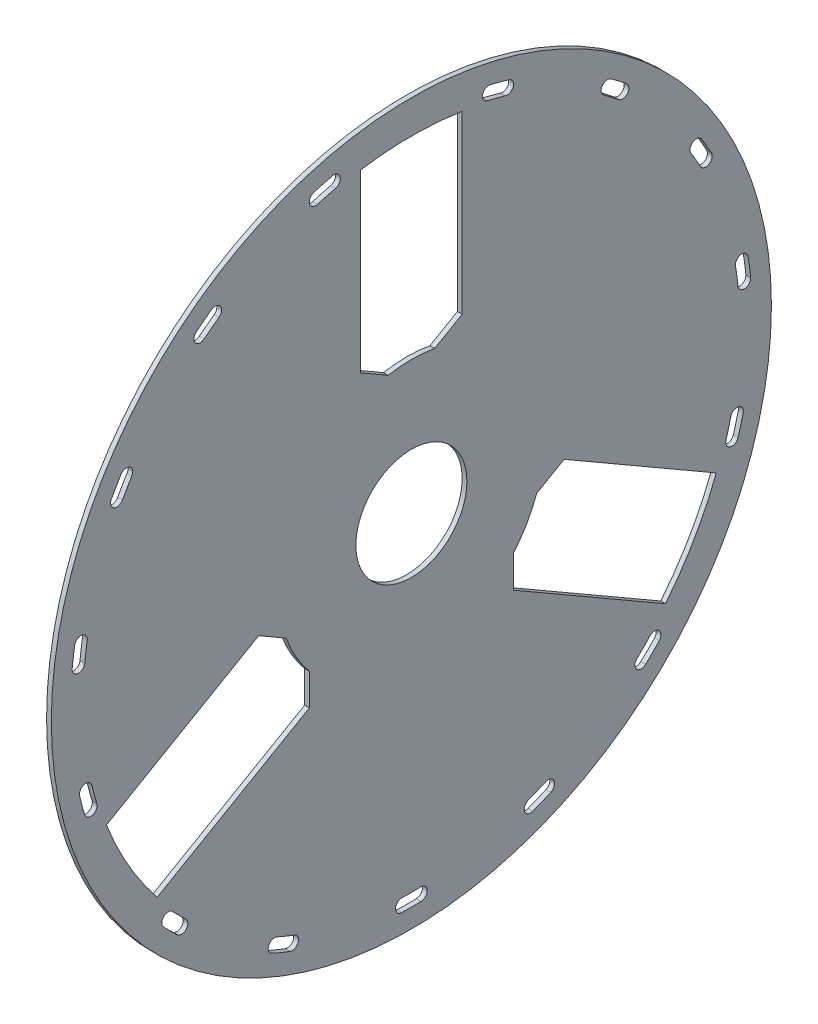
SolidWorks part; units mm, degrees
material "AISI 1020"
ref_plane "Спереди" through (0, 0, 0) normal (0, 0, 1) x (1, 0, 0)
ref_plane "Сверху" through (0, 0, 0) normal (0, 1, 0) x (1, 0, 0)
ref_plane "Справа" through (0, 0, 0) normal (1, 0, 0) x (0, 0, -1)
sketch "Эскиз1" plane through (0, 0, 0) normal (1, 0, 0) x (0, 0, -1)
  circle A0 centre (0, 0) radius 17.5
  circle A1 centre (0, 0) radius 113.5
  dimension "D1" = 227
  dimension "D2" = 35
extrude "Бобышка-Вытянуть1" add sketch "Эскиз1" along normal blind 1.5
sketch "Эскиз2" plane through (0, 0, 0) normal (-1, 0, 0) x (0, 0, 1)
  line L0 (0, 0) -> (0, 122.0247) construction
  line L1 (0, 122.0247) -> (0, 0) construction
  line L2 (-16, 101.7497) -> (-16, 46.3537)
  line L3 (-16, 46.3537) -> (-7.3397, 41.3537)
  line L4 (16, 46.3537) -> (7.3397, 41.3537)
  line L5 (16, 101.7497) -> (16, 46.3537)
  line L6 (96.1178, -37.0184) -> (48.1435, -9.3204)
  line L7 (80.1178, -64.7313) -> (32.1435, -37.0333)
  line L8 (32.1435, -37.0333) -> (32.1435, -27.0333)
  line L9 (48.1435, -9.3204) -> (39.4832, -14.3204)
  line L10 (-80.1178, -64.7313) -> (-32.1435, -37.0333)
  line L11 (-96.1178, -37.0184) -> (-48.1435, -9.3204)
  line L12 (-48.1435, -9.3204) -> (-39.4832, -14.3204)
  line L13 (-32.1435, -37.0333) -> (-32.1435, -27.0333)
  arc A0 (16, 101.7497) -> (-16, 101.7497) centre (0, 0) ccw
  arc A1 (7.3397, 41.3537) -> (-7.3397, 41.3537) centre (0, 0) ccw
  arc A2 (80.1178, -64.7313) -> (96.1178, -37.0184) centre (0, 0) ccw
  arc A3 (32.1435, -27.0333) -> (39.4832, -14.3204) centre (0, 0) ccw
  arc A4 (-96.1178, -37.0184) -> (-80.1178, -64.7313) centre (0, 0) ccw
  arc A5 (-39.4832, -14.3204) -> (-32.1435, -27.0333) centre (0, 0) ccw
  point P24 (0, 0)
  dimension "D1" = 206
  dimension "D2" = 84
  dimension "D6" = 61
  dimension "D3" = 32
  dimension "D4" = 120
  dimension "D5" = 10
  dimension "D7" = 3
extrude "Вырез-Вытянуть1" cut sketch "Эскиз2" against normal through all
sketch "Эскиз3" plane through (0, 0, 0) normal (-1, 0, 0) x (0, 0, 1)
  line L0 (0, 0) -> (0, -127.1913) construction
  line L1 (-40.3731, -97.4693) -> (0, 0) construction
  line L2 (0, 0) -> (-74.5998, -74.5998) construction
  circle A0 centre (0, 0) radius 103.5 construction
  arc A1 (-72.4483, -76.6909) -> (-76.6909, -72.4483) centre (0, 0) cw construction
  arc A2 (-78.1448, -73.8217) -> (-73.8217, -78.1448) centre (0, 0) ccw
  arc A3 (-75.2371, -71.0749) -> (-71.0749, -75.2371) centre (0, 0) ccw
  arc A4 (-75.2371, -71.0749) -> (-78.1448, -73.8217) centre (-76.6909, -72.4483) ccw
  arc A5 (-73.8217, -78.1448) -> (-71.0749, -75.2371) centre (-72.4483, -76.6909) ccw
  arc A6 (-43.1284, -96.2818) -> (-37.5851, -98.5779) centre (0, 0) ccw construction
  arc A7 (-43.946, -98.1071) -> (-38.2977, -100.4467) centre (0, 0) ccw
  arc A8 (-42.3108, -94.4566) -> (-36.8726, -96.7091) centre (0, 0) ccw
  arc A9 (-42.3108, -94.4566) -> (-43.946, -98.1071) centre (-43.1284, -96.2818) ccw
  arc A10 (-38.2977, -100.4467) -> (-36.8726, -96.7091) centre (-37.5851, -98.5779) ccw
  arc A11 (-3, -105.4573) -> (3, -105.4573) centre (0, 0) ccw construction
  arc A12 (-3.0569, -107.4565) -> (3.0569, -107.4565) centre (0, 0) ccw
  arc A13 (-2.9431, -103.4581) -> (2.9431, -103.4581) centre (0, 0) ccw
  arc A14 (-2.9431, -103.4581) -> (-3.0569, -107.4565) centre (-3, -105.4573) ccw
  arc A15 (3.0569, -107.4565) -> (2.9431, -103.4581) centre (3, -105.4573) ccw
  circle A17 centre (0, 0) radius 113.5 construction
  arc A18 (43.1284, -96.2818) -> (37.5851, -98.5779) centre (0, 0) cw construction
  arc A19 (43.946, -98.1071) -> (38.2977, -100.4467) centre (0, 0) cw
  arc A20 (42.3108, -94.4566) -> (36.8726, -96.7091) centre (0, 0) cw
  arc A21 (42.3108, -94.4566) -> (43.946, -98.1071) centre (43.1284, -96.2818) cw
  arc A22 (38.2977, -100.4467) -> (36.8726, -96.7091) centre (37.5851, -98.5779) cw
  arc A23 (72.4483, -76.6909) -> (76.6909, -72.4483) centre (0, 0) ccw construction
  arc A24 (78.1448, -73.8217) -> (73.8217, -78.1448) centre (0, 0) cw
  arc A25 (75.2371, -71.0749) -> (71.0749, -75.2371) centre (0, 0) cw
  arc A26 (75.2371, -71.0749) -> (78.1448, -73.8217) centre (76.6909, -72.4483) cw
  arc A27 (73.8217, -78.1448) -> (71.0749, -75.2371) centre (72.4483, -76.6909) cw
  point P7 (-74.5998, -74.5998)
  point P12 (-40.3731, -97.4693)
  point P20 (0, -105.5)
  point P32 (40.3731, -97.4693)
  point P41 (74.5998, -74.5998)
  dimension "D1" = 207
  dimension "D2" = 6
  dimension "D3" = 2
  dimension "D4" = 6
  dimension "D5" = 45
  dimension "D6" = 22.5
extrude "Вырез-Вытянуть2" cut sketch "Эскиз3" against normal through all
pattern_circular "Круговой массив1" count 3 over 360 about axis through (0, 0, 0) along (1, 0, 0) of "Вырез-Вытянуть2"
sketch "Эскиз4" plane through (0, 0, 0) normal (-1, 0, 0) x (0, 0, 1)
  line L0 (0, 0) -> (76.4331, 132.3859) construction
  line L1 (16, 46.3537) -> (16, 101.7497) construction
  line L2 (-32.1998, 145.6076) -> (208.0073, 6.924)
  line L3 (208.0073, 6.924) -> (98.0073, -183.6016)
  line L4 (98.0073, -183.6016) -> (-218.0858, -1.1052)
  line L5 (-218.0858, -1.1052) -> (-32.1998, 145.6076)
  dimension "D1" = 30
  dimension "D2" = 110
  dimension "D3" = 110
extrude "Вырез-Вытянуть3" [suppressed] cut sketch "Эскиз4" against normal through all flip side to cut
